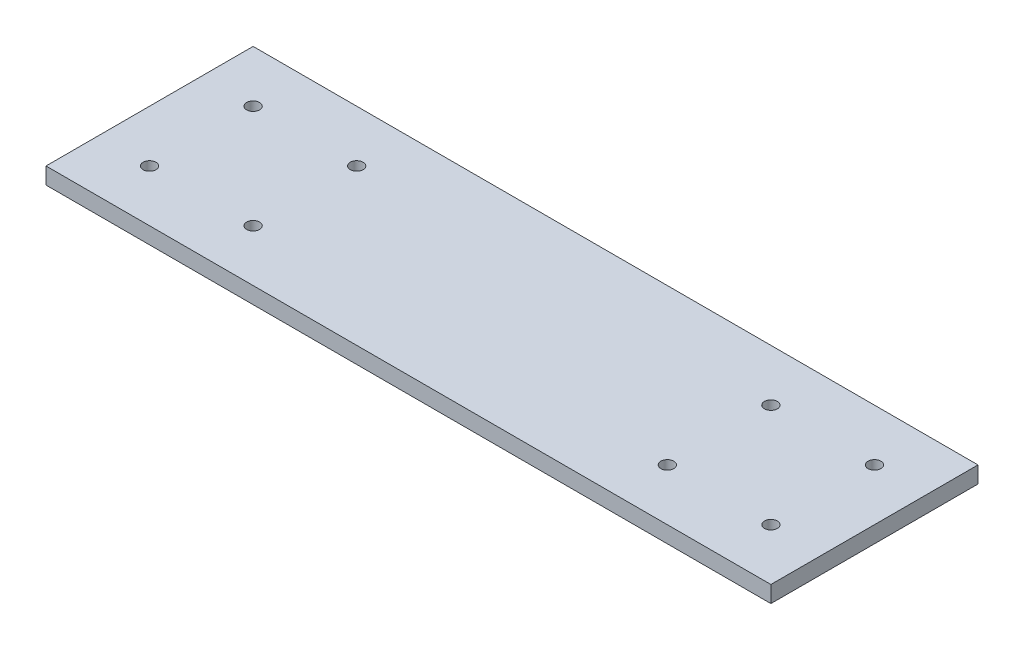
SolidWorks part; units mm, degrees
material "6061-T6 (SS)"
ref_plane "Front Plane" through (0, 0, 0) normal (0, 0, 1) x (1, 0, 0)
ref_plane "Top Plane" through (0, 0, 0) normal (0, 1, 0) x (1, 0, 0)
ref_plane "Right Plane" through (0, 0, 0) normal (1, 0, 0) x (0, 0, -1)
sketch "Sketch1" plane through (0, 0, 0) normal (0, 1, 0) x (1, 0, 0)
  line L1 (0, 0) -> (304.8, 0)
  line L2 (0, 0) -> (0, 50.8)
  line L3 (0, 50.8) -> (304.8, 50.8)
  line L4 (304.8, 0) -> (304.8, 50.8)
  dimension "D1" = 50.8
  dimension "D2" = 304.8
extrude "Boss-Extrude1" add sketch "Sketch1" along normal blind 4.064
hole_wizard "1/8 (0.125) Diameter Hole1" positions "Sketch3" profile "Sketch2" hole size "1/8" standard "ANSI Inch" end condition through all
sketch "Sketch3" plane through (0, 4.064, 0) normal (0, 1, 0) x (1, 0, 0)
  line L1 (12.7, 12.7) -> (38.1, 12.7) construction
  line L2 (12.7, 12.7) -> (12.7, 38.1) construction
  line L3 (12.7, 38.1) -> (38.1, 38.1) construction
  line L4 (38.1, 12.7) -> (38.1, 38.1) construction
  line L5 (0, 50.8) -> (0, 0) construction
  line L6 (304.8, 50.8) -> (0, 50.8) construction
  line L7 (50.8, 0) -> (50.8, 50.8) construction
  line L8 (0, 0) -> (304.8, 0) construction
  line L10 (127, 0) -> (127, 50.8) construction
  line L12 (177.8, 0) -> (177.8, 50.8) construction
  line L15 (139.7, 12.7) -> (165.1, 12.7) construction
  line L16 (139.7, 12.7) -> (139.7, 38.1) construction
  line L17 (139.7, 38.1) -> (165.1, 38.1) construction
  line L18 (165.1, 12.7) -> (165.1, 38.1) construction
  line L19 (139.7, 25.4) -> (127, 25.4) construction
  point P1 (12.7, 12.7)
  point P2 (38.1, 38.1)
  point P69 (12.7, 38.1)
  point P70 (38.1, 12.7)
  point P97 (139.7, 12.7)
  point P98 (165.1, 38.1)
  point P163 (139.7, 38.1)
  point P164 (165.1, 12.7)
  dimension "D1" = 12.7
  dimension "D2" = 12.7
  dimension "D3" = 25.4
  dimension "D4" = 25.4
  dimension "D5" = 76.2
  dimension "D6" = 50.8
  dimension "D7" = 50.8
  dimension "D8" = 25.4
  dimension "D9" = 25.4
  dimension "D10" = 12.7
sketch "Sketch2" plane through (12.7, 4.064, -12.7) normal (1, 0, 0) x (0, 0, 1)
  line L0 (0, 0) -> (0, 4.064)
  line L1 (0, 4.064) -> (1.5875, 4.064)
  line L2 (1.5875, 4.064) -> (1.5875, 0)
  line L5 (1.5875, 0) -> (0, 0)
  line L11 (0, -6.35) -> (0, 107.95) construction
  dimension "Thru Hole Dia." = 3.175
  dimension "Thru Hole Depth" = 4.064
sketch "Sketch4" plane through (0, 4.064, 0) normal (0, 1, 0) x (1, 0, 0)
  line L0 (0, 0) -> (304.8, 0) construction
  line L1 (304.8, 50.8) -> (177.8, 50.8)
  line L2 (304.8, 50.8) -> (304.8, 0)
  line L3 (304.8, 0) -> (177.8, 0)
  line L4 (177.8, 50.8) -> (177.8, 0)
  line L5 (165.1, 12.7) -> (165.1, 38.1) construction
  dimension "D1" = 12.7
extrude "Cut-Extrude1" cut sketch "Sketch4" against normal through all
